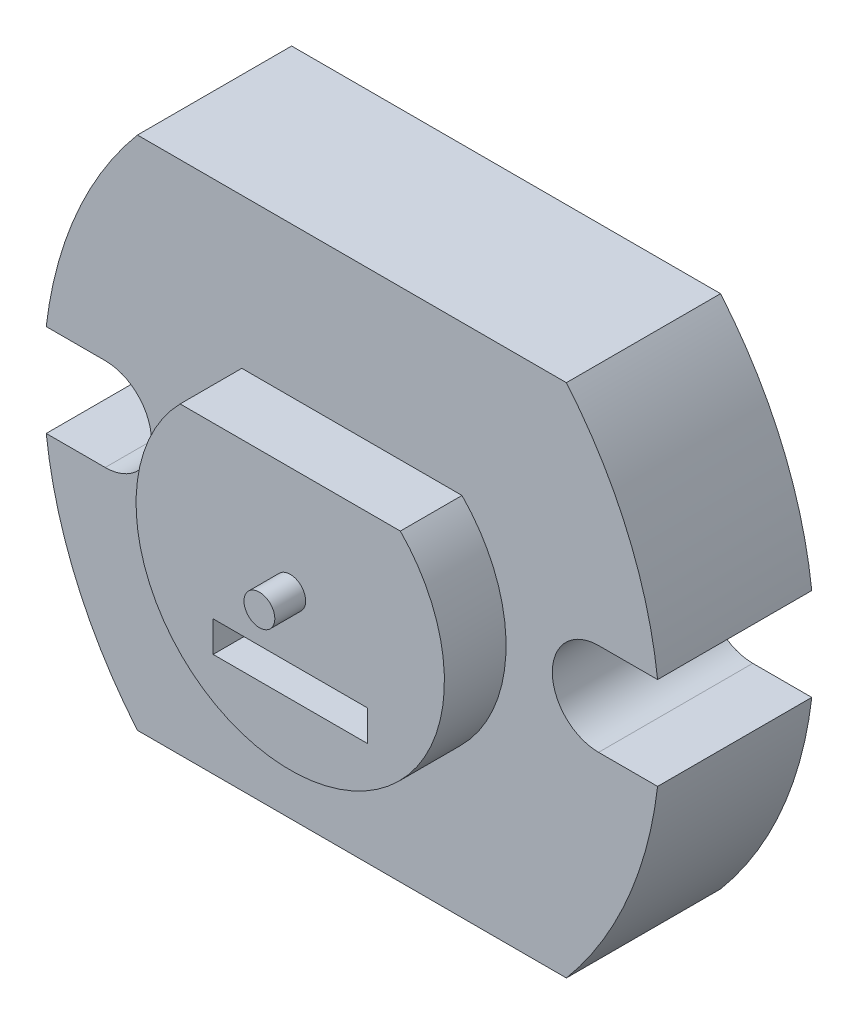
SolidWorks part; units mm, degrees
ref_plane "Front Plane" through (0, 0, 0) normal (0, 0, 1) x (1, 0, 0)
ref_plane "Top Plane" through (0, 0, 0) normal (0, 1, 0) x (1, 0, 0)
ref_plane "Right Plane" through (0, 0, 0) normal (1, 0, 0) x (0, 0, -1)
sketch "Sketch1" plane through (0, 0, 0) normal (0, 0, 1) x (1, 0, 0)
  line L0 (-10, 0) -> (10, 0)
  line L1 (0, 8.36) -> (0, 0) construction
  line L2 (-6.9554, 8.36) -> (6.9554, 8.36)
  line L4 (-6.9554, -8.36) -> (6.9554, -8.36)
  line L6 (-10, 0) -> (10, 0) construction
  arc A0 (-6.9554, -8.36) -> (-6.9554, 8.36) centre (3, 0) cw
  arc A1 (6.9554, -8.36) -> (6.9554, 8.36) centre (-3, 0) ccw
  point P10 (-10, 0)
  dimension "D5" = 13
  dimension "D1" = 8.36
  dimension "D3" = 10
  dimension "D2" = 13.9108
extrude "Boss-Extrude2" add sketch "Sketch1" along normal blind 5 contours L0 A1 L2 A0 | L4 A1 L0 A0
sketch "Sketch2" plane through (0, 0, 5) normal (0, 0, 1) x (1, 0, 0)
  line L0 (0, 8.36) -> (0, -8.36) construction
  line L1 (-6.9554, 8.36) -> (6.9554, 8.36) construction
  line L2 (-6.9554, -8.36) -> (6.9554, -8.36) construction
  line L3 (-10, 0) -> (10, 0) construction
  line L4 (-8, 1.5) -> (-9.9132, 1.5)
  line L5 (-8, -1.5) -> (-9.9132, -1.5)
  line L6 (8, -1.5) -> (9.9132, -1.5)
  line L7 (8, 1.5) -> (9.9132, 1.5)
  line L8 (-9.9132, 1.5) -> (-10.3171, 1.5)
  line L9 (-9.9132, -1.5) -> (-10.3171, -1.5)
  line L10 (9.9132, 1.5) -> (10.3171, 1.5)
  line L11 (9.9132, -1.5) -> (10.3171, -1.5)
  arc A0 (-8, -1.5) -> (-8, 1.5) centre (-8, 0) ccw
  arc A2 (6.9554, -8.36) -> (6.9554, 8.36) centre (-3, 0) ccw construction
  arc A3 (-6.9554, 8.36) -> (-6.9554, -8.36) centre (3, 0) ccw construction
  arc A4 (8, -1.5) -> (8, 1.5) centre (8, 0) cw
  arc A5 (-10.3171, 1.5) -> (-10.3171, -1.5) centre (0, 0) ccw
  arc A6 (10.3171, -1.5) -> (10.3171, 1.5) centre (0, 0) ccw
  dimension "D1" = 3
  dimension "D3" = 20.8512
  dimension "D2" = 2
extrude "Cut-Extrude1" cut sketch "Sketch2" against normal blind 5
sketch "Sketch3" plane through (0, 0, 5) normal (0, 0, 1) x (1, 0, 0)
  circle A0 centre (0, 0) radius 0.5
  dimension "D1" = 1
extrude "Boss-Extrude3" add sketch "Sketch3" along normal blind 3
sketch "Sketch4" plane through (0, 0, 5) normal (0, 0, 1) x (1, 0, 0)
  line L0 (0, -8.36) -> (0, 8.36) construction
  line L1 (-6.9554, -8.36) -> (6.9554, -8.36) construction
  line L2 (-6.9554, 8.36) -> (6.9554, 8.36) construction
  line L3 (-3.5707, 3.5) -> (3.5707, 3.5)
  arc A0 (-3.5707, 3.5) -> (3.5707, 3.5) centre (0, 0) ccw
  dimension "D1" = 10
  dimension "D2" = 3.5
extrude "Boss-Extrude4" add sketch "Sketch4" along normal blind 2
sketch "Sketch5" plane through (0, 0, 7) normal (0, 0, 1) x (1, 0, 0)
  line L0 (0, 3.5) -> (0, -5) construction
  line L2 (3.5707, 3.5) -> (-3.5707, 3.5) construction
  line L4 (-2.5, -2) -> (2.5, -2)
  line L5 (-2.5, -2) -> (-2.5, -3)
  line L6 (-2.5, -3) -> (2.5, -3)
  line L7 (2.5, -2) -> (2.5, -3)
  arc A0 (-3.5707, 3.5) -> (3.5707, 3.5) centre (0, 0) ccw construction
  point P11 (0, -3)
  point P12 (0, 0)
  dimension "D1" = 1
  dimension "D2" = 3
  dimension "3" = 5
extrude "Cut-Extrude2" cut sketch "Sketch5" against normal blind 2
